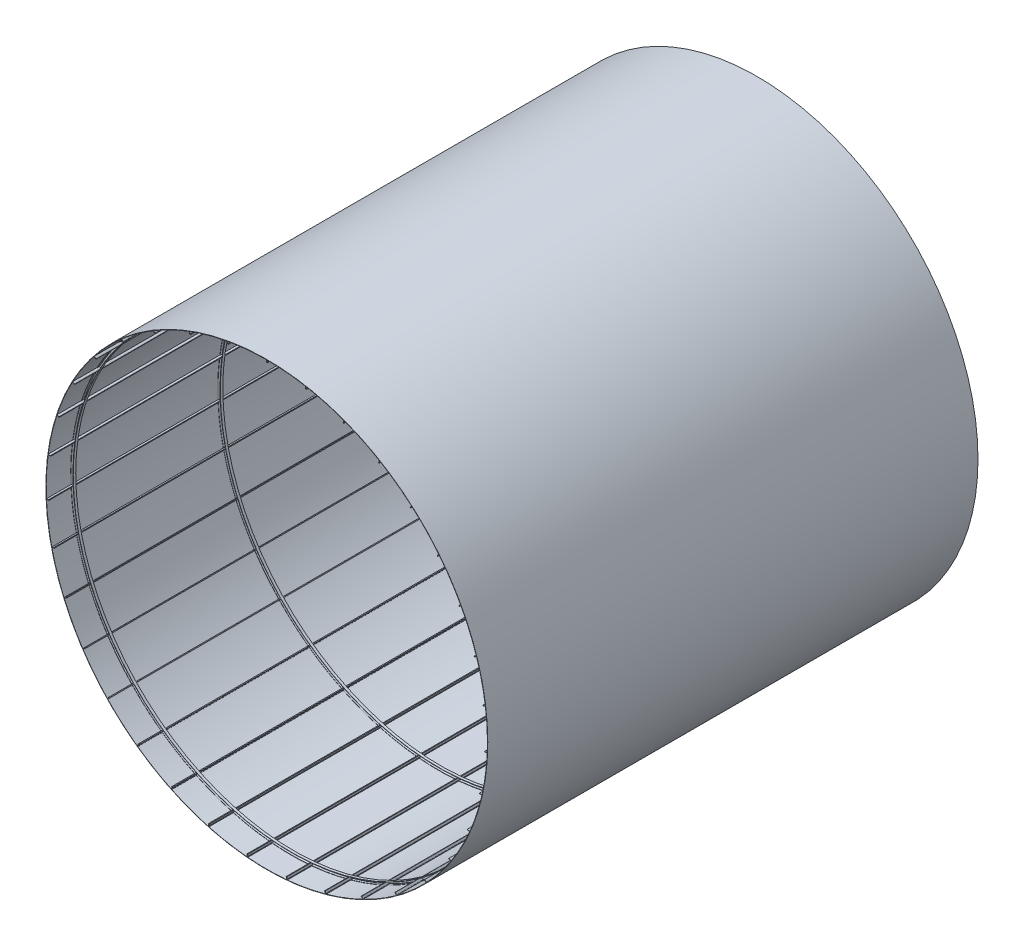
SolidWorks part; units mm, degrees
ref_plane "Front" through (0, 0, 0) normal (0, 0, 1) x (1, 0, 0)
ref_plane "Top" through (0, 0, 0) normal (0, 1, 0) x (1, 0, 0)
ref_plane "Right" through (0, 0, 0) normal (1, 0, 0) x (0, 0, -1)
sketch "Sketch1" plane through (0, 0, 0) normal (0, 0, 1) x (1, 0, 0)
  circle A0 centre (0, 0) radius 900
  circle A1 centre (0, 0) radius 901.5
  dimension "D1" = 1800
  dimension "D2" = 1803
extrude "Boss-Extrude1" add sketch "Sketch1" along normal blind 2000
sketch "Sketch2" plane through (0, 0, 0) normal (0, 0, 1) x (1, 0, 0)
  line L1 (-3, 900) -> (0, 900)
  line L2 (-3, 900) -> (-3, 898.5)
  line L3 (-3, 898.5) -> (0, 898.5)
  line L4 (0, 900) -> (0, 898.5)
  line L5 (0, 898.5) -> (-1.5, 898.5)
  line L6 (0, 898.5) -> (0, 891.5)
  line L7 (0, 891.5) -> (-1.5, 891.5)
  line L8 (-1.5, 898.5) -> (-1.5, 891.5)
  line L9 (-1.5, 891.5) -> (1.5, 891.5)
  line L10 (-1.5, 891.5) -> (-1.5, 890)
  line L11 (-1.5, 890) -> (1.5, 890)
  line L12 (1.5, 891.5) -> (1.5, 890)
  circle A0 centre (0, 0) radius 900 construction
  point P10 (-440.099, 327.2264)
  point P11 (-408.1984, 386.4326)
  point P12 (0, 0)
  point P14 (0, 0)
  dimension "D1" = 1.5
  dimension "D2" = 1.5
  dimension "D3" = 1.5
  dimension "D4" = 10
  dimension "D5" = 3
  dimension "D6" = 3
extrude "Boss-Extrude2" add sketch "Sketch2" along normal blind 2000 contours L3 L8 L7 L6 | L12 L9 L7 L10 L11 | L4 L1 L2 L3
pattern_circular "CirPattern1" count 35 over 360 about axis through (0, 0, 0) along (0, 0, 1) of "Boss-Extrude2"
sketch "Sketch3" plane through (0, 0, 0) normal (0, 1, 0) x (1, 0, 0)
  line L0 (0, 0) -> (0, -391.7092) construction
  line L1 (900, -100.175) -> (899, -100.175)
  line L2 (900, -100.175) -> (900, -89.975)
  line L3 (900, -89.975) -> (899, -89.975)
  line L4 (899, -100.175) -> (899, -89.975)
  line L5 (899, -89.975) -> (890.6, -89.975)
  line L6 (899, -89.975) -> (899, -90.975)
  line L7 (899, -90.975) -> (890.6, -90.975)
  line L8 (890.6, -89.975) -> (890.6, -90.975)
  line L9 (890.6, -89.975) -> (889.6, -89.975)
  line L10 (890.6, -89.975) -> (890.6, -100.175)
  line L11 (890.6, -100.175) -> (889.6, -100.175)
  line L12 (889.6, -89.975) -> (889.6, -100.175)
  dimension "D1" = 1
  dimension "D2" = 1
  dimension "D3" = 1
  dimension "D4" = 10.2
  dimension "D5" = 10.2
  dimension "D6" = 10.4
  dimension "D7" = 900
revolve "Revolve2" add sketch "Sketch3" angle 360 about L0
pattern_linear "LPattern1" count 4 spacing 600 along (0, 0, 1) of "Revolve2"
